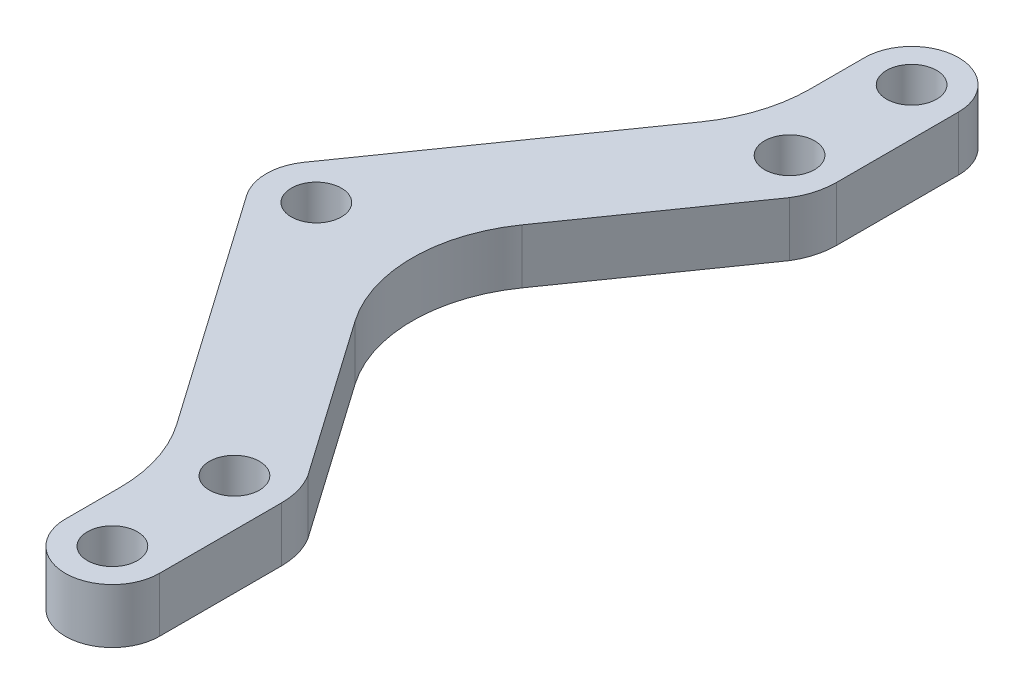
SolidWorks part; units mm, degrees
material "CARBON FIBER TEST"
ref_plane "Front Plane" through (0, 0, 0) normal (0, 0, 1) x (1, 0, 0)
ref_plane "Top Plane" through (0, 0, 0) normal (0, 1, 0) x (1, 0, 0)
ref_plane "Right Plane" through (0, 0, 0) normal (1, 0, 0) x (0, 0, -1)
sketch "Sketch1" plane through (0, 0, 0) normal (0, 1, 0) x (1, 0, 0)
  line L1 (-15.25, -15.25) -> (15.25, -15.25) construction
  line L2 (-15.25, -15.25) -> (-15.25, 15.25) construction
  line L3 (-15.25, 15.25) -> (15.25, 15.25) construction
  line L4 (15.25, -15.25) -> (15.25, 15.25) construction
  line L5 (-15.25, -15.25) -> (15.25, 15.25) construction
  line L6 (-15.25, 15.25) -> (15.25, -15.25) construction
  point P0 (0, 0)
  dimension "D1" = 30.5
sketch "Sketch5" plane through (0, 0, 0) normal (0, 1, 0) x (1, 0, 0)
  line L0 (0, -16) -> (0, 16)
  line L1 (0, 16) -> (-23, 16)
  line L2 (-23, 16) -> (-23, -16)
  line L3 (-23, -16) -> (0, -16)
  line L4 (-11.5, 16) -> (-11.5, -16) construction
  line L5 (-23, 0) -> (0, 0) construction
  point P4 (0, 0)
  point P10 (-15.25, -14.7545)
  dimension "D1" = 23
  dimension "D2" = 32
sketch "Sketch6" plane through (0, 0, 0) normal (0, 1, 0) x (-1, 0, 0)
  line L14 (23, -16) -> (23, 16) construction
  line L20 (23, -16) -> (23, 16) construction
  line L22 (23, 0) -> (0, 0) construction
  circle A2 centre (26, 0) radius 1.375 construction
  dimension "D7" = 3
  dimension "D8" = 2.75
sketch "Sketch2" plane through (0, 0, 0) normal (0, 1, 0) x (1, 0, 0)
  line L0 (-15.25, 15.25) -> (15.25, -15.25) construction
  line L5 (-12.6654, 21.9553) -> (-12.6654, 15.25)
  line L7 (-27.375, 0) -> (-28.75, 0)
  line L8 (-15.25, 15.25) -> (-16.1391, 13.9802) construction
  line L11 (-13.2335, 13.2335) -> (-22.5, 0)
  line L12 (-17.8346, 16.4553) -> (-28.2526, 1.5774)
  line L14 (-17.8346, 16.4553) -> (-17.8346, 21.9553)
  line L15 (-22.5, 0) -> (-24.625, 0)
  line L17 (-12.6654, 21.9553) -> (-17.8346, 21.9553) construction
  line L18 (-15.25, 15.25) -> (15.25, 15.25) construction
  arc A0 (-28.2526, 1.5774) -> (-28.75, 0) centre (-26, 0) ccw
  arc A1 (-24.625, 0) -> (-27.375, 0) centre (-26, 0) ccw
  arc A4 (-12.6654, 21.9553) -> (-17.8346, 21.9553) centre (-15.25, 21.9553) ccw
  arc A5 (-12.6654, 15.25) -> (-13.2335, 13.2335) centre (-16.5288, 15.25) cw
  dimension "D4" = 5.5
  dimension "D5" = 2.75
  dimension "D1" = 3.5
  dimension "D3" = 5.5
extrude "Boss-Extrude1" add sketch "Sketch2" along normal blind 3
sketch "Sketch3" plane through (0, 3, 0) normal (0, 1, 0) x (1, 0, 0)
  circle A0 centre (-15.25, 15.25) radius 1.375
  arc A1 (-24.625, 0) -> (-27.375, 0) centre (-26, 0) ccw construction
  circle A2 centre (-15.25, 21.9553) radius 1.375
extrude "Cut-Extrude1" cut sketch "Sketch3" against normal through all
mirror "Mirror2" about plane through (-22.5, 3, 0) normal (0, 0, -1) of "Cut-Extrude1", "Boss-Extrude1"
fillet "Fillet1" radius 8 3 edges at (-22.5, 1.5, 0) (-17.8346, 1.5, 16.4553) (-17.8346, 1.5, -16.4553)
